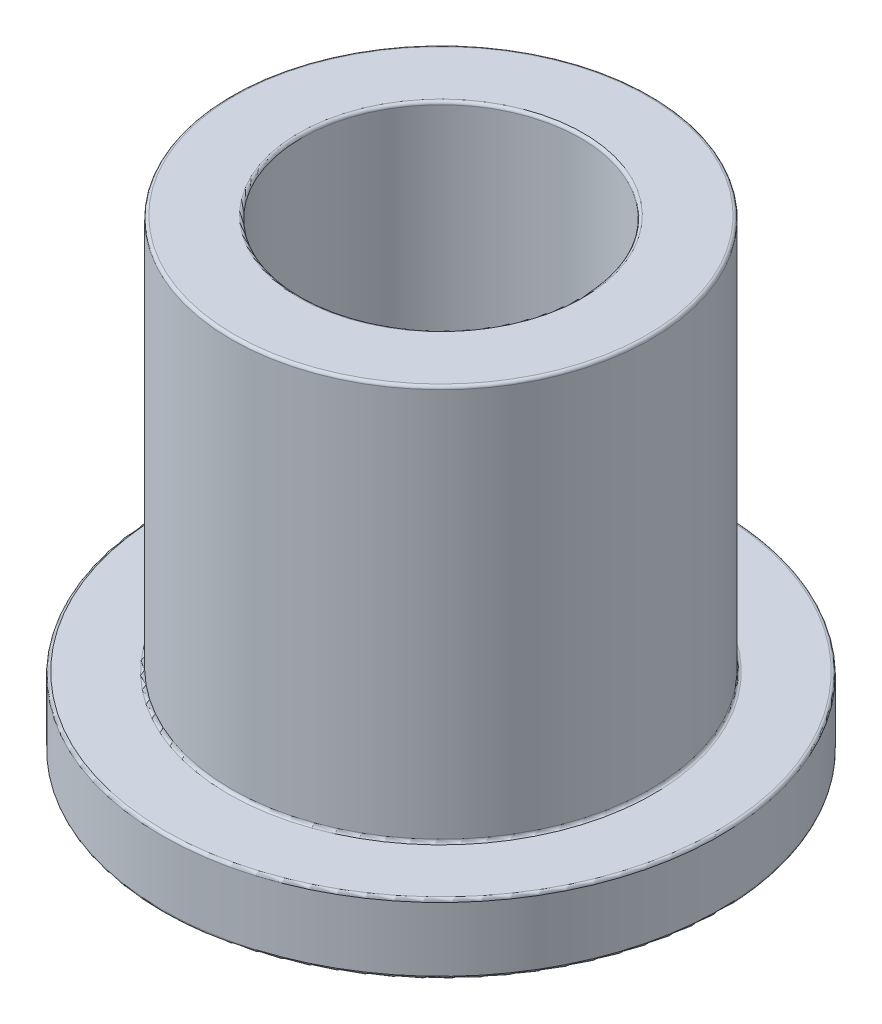
SolidWorks part; units mm, degrees
ref_plane "Front" through (0, 0, 0) normal (0, 0, 1) x (1, 0, 0)
ref_plane "Top" through (0, 0, 0) normal (0, 1, 0) x (1, 0, 0)
ref_plane "Right" through (0, 0, 0) normal (1, 0, 0) x (0, 0, -1)
sketch "Sketch1" plane through (0, 0, 0) normal (0, 1, 0) x (1, 0, 0)
  circle A0 centre (0, 0) radius 6.005
  circle A1 centre (0, 0) radius 9.015
  circle A2 centre (0, 0) radius 12
  dimension "ID" = 12.01
  dimension "OD" = 18.03
  dimension "FlangeOD" = 24
sketch "Sketch2" plane through (0, 0, 0) normal (1, 0, 0) x (0, 0, -1)
  line L0 (12, 0) -> (12, 3) construction
  line L1 (-9.015, 0) -> (-9.015, 20) construction
  line L8 (0, 0) -> (0, 20) construction
  point P5 (-12, 0)
  dimension "Flange Thickness" = 3
  dimension "Length" = 20
sketch "Sketch3" plane through (0, 0, 0) normal (0, 1, 0) x (1, 0, 0)
  circle A0 centre (0, 0) radius 6.005 construction
  circle A1 centre (0, 0) radius 9.015 construction
  circle A2 centre (0, 0) radius 6.005
  circle A3 centre (0, 0) radius 9.015
extrude "Boss-Extrude1" add sketch "Sketch3" along normal up to vertex (20 mm away) up to point (0, 20, 9.015)
sketch "Sketch4" plane through (0, 0, 0) normal (0, 1, 0) x (1, 0, 0)
  circle A0 centre (0, 0) radius 12 construction
  circle A1 centre (0, 0) radius 9.015 construction
  circle A2 centre (0, 0) radius 12
  circle A3 centre (0, 0) radius 9.015
extrude "Boss-Extrude2" add sketch "Sketch4" along normal up to vertex (3 mm away) up to point (0, 3, -12)
fillet "Fillet1" radius 0.125 6 edges at (0, 0, 6.005) (0, 0, 12) (0, 3, 9.015) (0, 3, 12) (0, 20, 6.005) (0, 20, 9.015)
